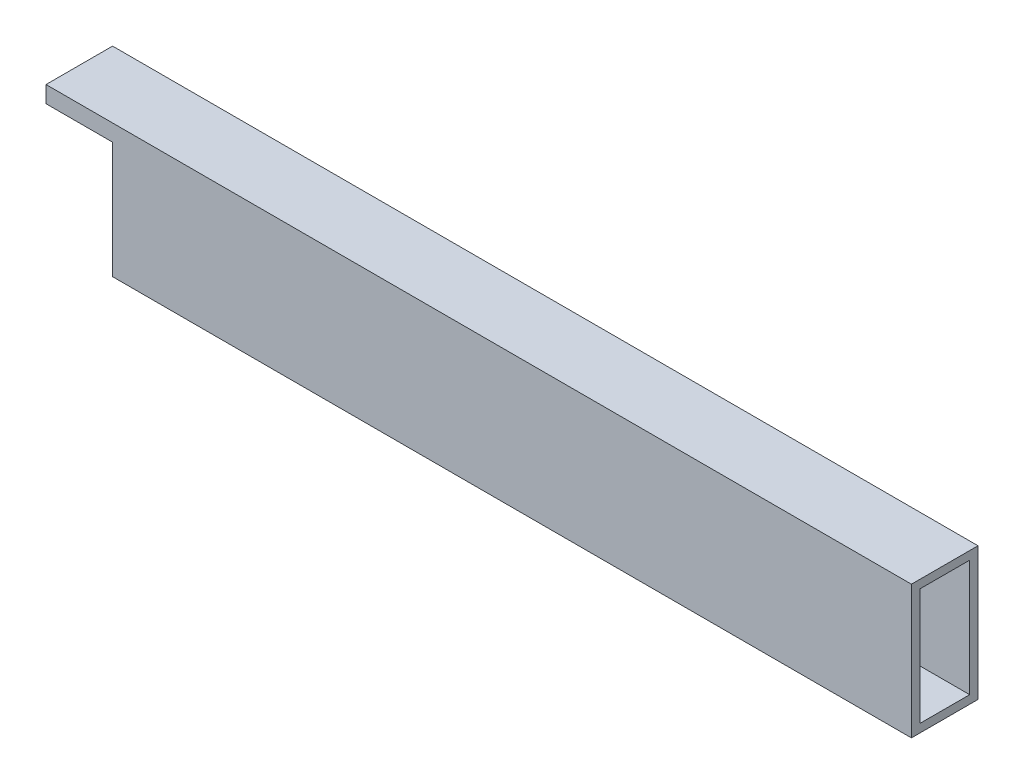
SolidWorks part; units mm, degrees
ref_plane "Front Plane" through (0, 0, 0) normal (0, 0, 1) x (1, 0, 0)
ref_plane "Top Plane" through (0, 0, 0) normal (0, 1, 0) x (1, 0, 0)
ref_plane "Right Plane" through (0, 0, 0) normal (1, 0, 0) x (0, 0, -1)
sketch "Sketch1" plane through (0, 0, 0) normal (0, 1, 0) x (1, 0, 0)
  line L0 (-330.2, 0) -> (0, 0)
  line L1 (0, 0) -> (0, -25.4)
  line L2 (0, -25.4) -> (-330.2, -25.4)
  line L3 (-330.2, -25.4) -> (-330.2, 0)
extrude "Boss-Extrude4" add sketch "Sketch1" along normal blind 50.8
sketch "Sketch5" plane through (-330.2, 0, 0) normal (-1, 0, 0) x (0, 0, 1)
  line L0 (25.4, 50.8) -> (0, 50.8) construction
  line L1 (3.175, 47.625) -> (22.225, 47.625)
  line L2 (3.175, 47.625) -> (3.175, 3.175)
  line L3 (3.175, 3.175) -> (22.225, 3.175)
  line L4 (22.225, 47.625) -> (22.225, 3.175)
  line L5 (0, 50.8) -> (0, 0) construction
  line L6 (25.4, 50.8) -> (25.4, 0) construction
  line L7 (0, 0) -> (25.4, 0) construction
  point P4 (12.7, 50.8)
  dimension "D1" = 3.175
  dimension "D2" = 3.175
  dimension "D3" = 3.175
  dimension "D4" = 3.175
extrude "Cut-Extrude1" cut sketch "Sketch5" against normal blind 330.2
sketch "Sketch7" plane through (0, 0, 0) normal (0, 0, -1) x (-1, 0, 0)
  line L0 (330.2, 44.45) -> (304.8, 44.45)
  line L2 (330.2, 50.8) -> (330.2, 0)
  line L3 (330.2, 0) -> (304.8, 0)
  line L4 (0, 0) -> (330.2, 0) construction
  line L5 (304.8, 44.45) -> (304.8, 0)
  line L6 (304.8, 0) -> (330.2, 0)
  line L7 (304.8, 0) -> (330.2, 0)
  line L8 (0, 50.8) -> (330.2, 50.8) construction
  line M7 (0, 0) -> (330.2, 0)
  line M8 (330.2, 0) -> (330.2, 50.8)
  dimension "D1" = 25.4
  dimension "D2" = 6.35
extrude "Cut-Extrude4" cut sketch "Sketch7" against normal blind 31.496 contours L0 L5 M7 M8
